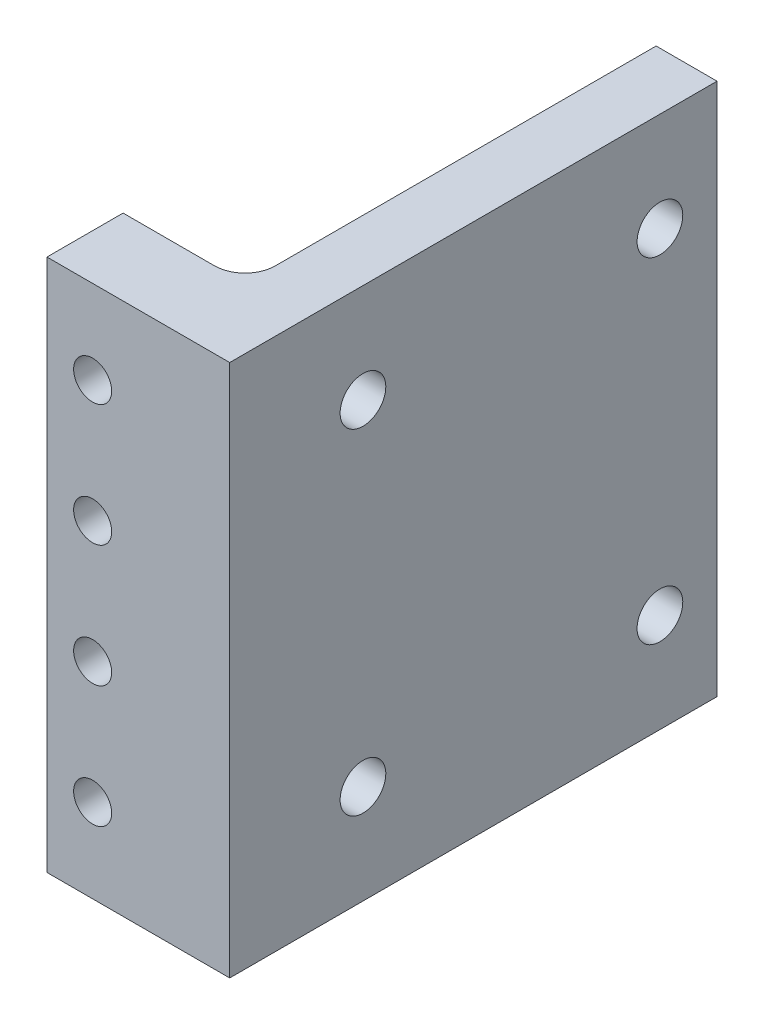
SolidWorks part; units mm, degrees
ref_plane "Plan de face" through (0, 0, 0) normal (0, 0, 1) x (1, 0, 0)
ref_plane "Plan de dessus" through (0, 0, 0) normal (0, 1, 0) x (1, 0, 0)
ref_plane "Plan de droite" through (0, 0, 0) normal (1, 0, 0) x (0, 0, -1)
sketch "Esquisse1" plane through (0, 0, 0) normal (0, 0, 1) x (1, 0, 0)
  line L0 (0, 0) -> (12, 0)
  line L1 (12, 0) -> (12, 35)
  line L5 (0, 35) -> (0, 0)
  line L6 (0, 35) -> (12, 35)
extrude "Boss.-Extru.1" add sketch "Esquisse1" along normal blind 5
sketch "Esquisse2" plane through (0, 0, 0) normal (0, 0, -1) x (-1, 0, 0)
  line L0 (0, 0) -> (-12, 0) construction
  line L1 (-12, 35) -> (-8, 35)
  line L2 (-12, 35) -> (-12, 0)
  line L3 (-12, 0) -> (-8, 0)
  line L4 (-8, 35) -> (-8, 0)
extrude "Boss.-Extru.2" add sketch "Esquisse2" along normal blind 27
sketch "Esquisse3" plane through (0, 0, 5) normal (0, 0, 1) x (1, 0, 0)
  line L0 (0, 35) -> (0, 0) construction
  line L1 (12, 35) -> (0, 35) construction
  line L2 (0, 0) -> (12, 0) construction
  line L3 (3, 29.5) -> (3, 35) construction
  line L4 (3, 5.5) -> (3, 0) construction
  circle A0 centre (3, 5.5) radius 1.25
  circle A1 centre (3, 13.5) radius 1.25
  circle A2 centre (3, 21.5) radius 1.25
  circle A3 centre (3, 29.5) radius 1.25
extrude "Enlèv. mat.-Extru.1" cut sketch "Esquisse3" against normal through all
sketch "Esquisse4" plane through (8, 0, 0) normal (-1, 0, 0) x (0, 0, 1)
  line L0 (-23.25, 35) -> (-23.25, 28.5) construction
  line L1 (-27, 35) -> (0, 35) construction
  line L2 (-23.25, 28.5) -> (-23.25, 6.5) construction
  line L3 (-23.25, 6.5) -> (-23.25, 0) construction
  line L4 (-27, 0) -> (0, 0) construction
  line L5 (-27, 28.5) -> (-23.25, 28.5) construction
  line L6 (-27, 0) -> (-27, 35) construction
  line L7 (-23.25, 28.5) -> (-3.75, 28.5) construction
  line L8 (-3.75, 28.5) -> (0, 28.5) construction
  line L9 (0, 0) -> (0, 35) construction
  line L10 (-3.75, 28.5) -> (-3.75, 6.5) construction
  line L11 (-3.75, 6.5) -> (-23.25, 6.5) construction
  circle A0 centre (-23.25, 28.5) radius 1.5
  circle A1 centre (-3.75, 28.5) radius 1.5
  circle A2 centre (-23.25, 6.5) radius 1.5
  circle A3 centre (-3.75, 6.5) radius 1.5
extrude "Enlèv. mat.-Extru.2" cut sketch "Esquisse4" against normal through all
fillet "Congé1" radius 2 1 edges at (8, 17.5, 0)
